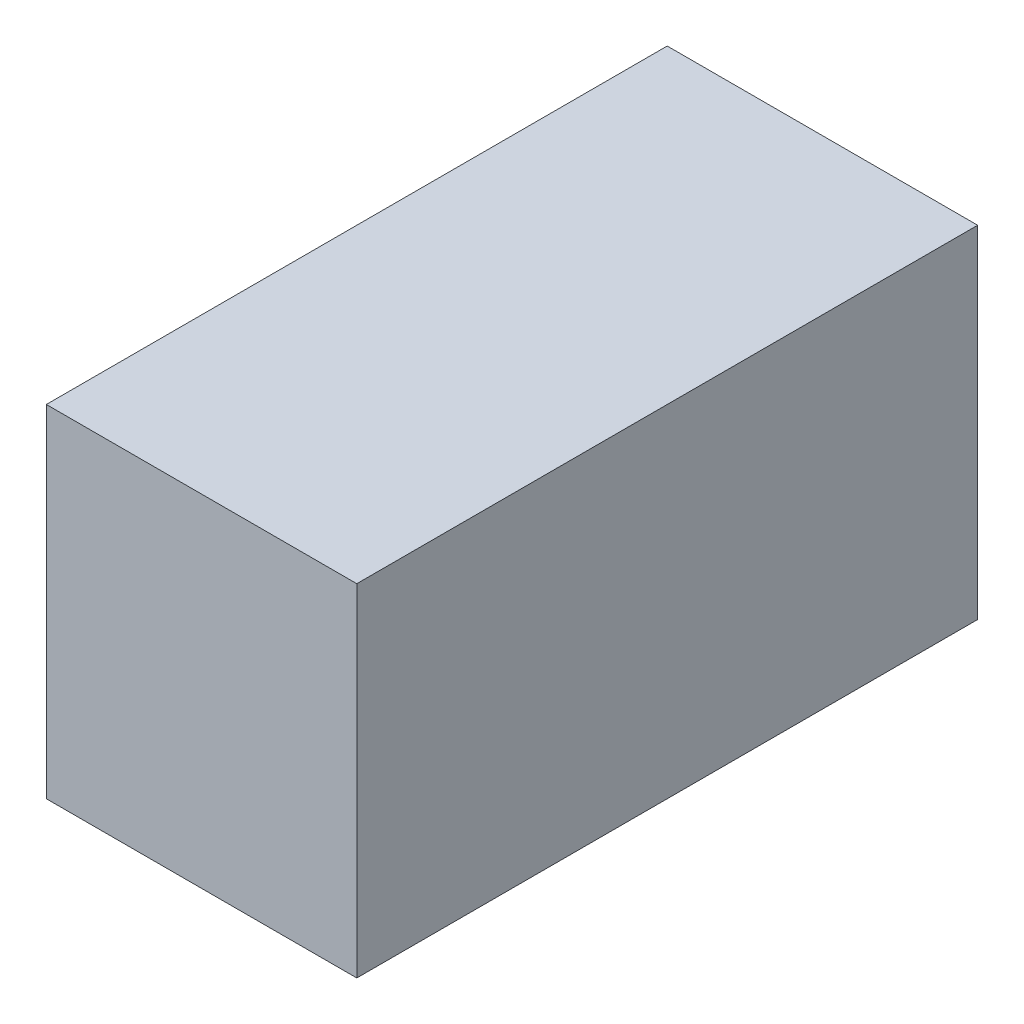
SolidWorks part; units mm, degrees
ref_plane "Front Plane" through (0, 0, 0) normal (0, 0, 1) x (1, 0, 0)
ref_plane "Top Plane" through (0, 0, 0) normal (0, 1, 0) x (1, 0, 0)
ref_plane "Right Plane" through (0, 0, 0) normal (1, 0, 0) x (0, 0, -1)
sketch "Sketch1" plane through (0, 0, 0) normal (0, 1, 0) x (1, 0, 0)
  line L1 (0, 0) -> (0.5, 0)
  line L2 (0, 0) -> (0, 1)
  line L3 (0, 1) -> (0.5, 1)
  line L4 (0.5, 0) -> (0.5, 1)
  dimension "D1" = 0.5
  dimension "D2" = 1
extrude "Boss-Extrude2" add sketch "Sketch1" along normal blind 0.55
